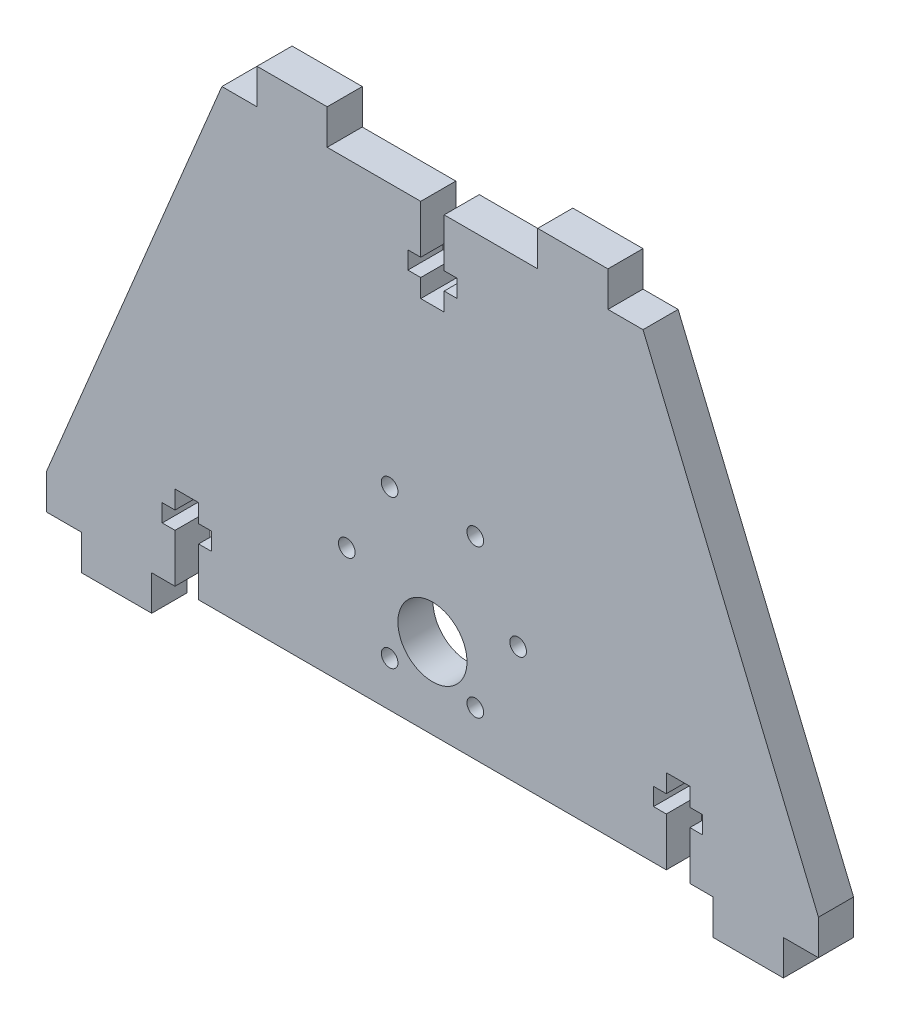
SolidWorks part; units mm, degrees
ref_plane "Front Plane" through (0, 0, 0) normal (0, 0, 1) x (1, 0, 0)
ref_plane "Top Plane" through (0, 0, 0) normal (0, 1, 0) x (1, 0, 0)
ref_plane "Right Plane" through (0, 0, 0) normal (1, 0, 0) x (0, 0, -1)
sketch "Sketch1" plane through (0, 0, 0) normal (0, 0, 1) x (1, 0, 0)
  line L1 (-69.85, 41.275) -> (69.85, 41.275)
  line L2 (-69.85, 41.275) -> (-69.85, -41.275)
  line L3 (-69.85, -41.275) -> (69.85, -41.275)
  line L4 (69.85, 41.275) -> (69.85, -41.275)
  line L5 (-69.85, 41.275) -> (69.85, -41.275) construction
  line L6 (-69.85, -41.275) -> (69.85, 41.275) construction
  point P0 (0, 0)
  dimension "D1" = 82.55
  dimension "D2" = 139.7
extrude "Boss-Extrude1" add sketch "Sketch1" along normal blind 6.35
sketch "Sketch2" plane through (0, 0, 0) normal (0, 0, -1) x (-1, 0, 0)
  line L0 (69.85, -41.275) -> (-69.85, -41.275) construction
  line L1 (-63.5, -41.275) -> (-50.8, -41.275)
  line L2 (-63.5, -41.275) -> (-63.5, -47.625)
  line L3 (-63.5, -47.625) -> (-50.8, -47.625)
  line L4 (-50.8, -41.275) -> (-50.8, -47.625)
  line L5 (-69.85, -41.275) -> (-69.85, 41.275) construction
  line L6 (-69.85, 41.275) -> (69.85, 41.275) construction
  line L7 (-31.75, 41.275) -> (-19.05, 41.275)
  line L8 (-31.75, 41.275) -> (-31.75, 47.625)
  line L9 (-31.75, 47.625) -> (-19.05, 47.625)
  line L10 (-19.05, 41.275) -> (-19.05, 47.625)
  dimension "D1" = 6.35
  dimension "D2" = 12.7
  dimension "D3" = 6.35
  dimension "D4" = 6.35
  dimension "D5" = 12.7
  dimension "D6" = 38.1
extrude "Boss-Extrude2" add sketch "Sketch2" against normal blind 6.35
sketch "Sketch3" plane through (0, 0, 0) normal (0, 0, -1) x (-1, 0, 0)
  line L1 (-46.5836, -41.275) -> (-46.5836, -32.512)
  line L2 (69.85, -41.275) -> (-50.8, -41.275) construction
  line L3 (-46.5836, -32.512) -> (-48.895, -32.512)
  line L4 (-48.895, -32.512) -> (-48.895, -29.337)
  line L5 (-48.895, -29.337) -> (-46.5836, -29.337)
  line L6 (-46.5836, -29.337) -> (-46.5836, -26.035)
  line L7 (-46.5836, -26.035) -> (-42.3164, -26.035)
  line L8 (-44.45, -26.035) -> (-44.45, -41.275) construction
  line L9 (-42.3164, -41.275) -> (-46.5836, -41.275)
  line L10 (-63.5, -47.625) -> (-50.8, -47.625) construction
  line L11 (-42.3164, -29.337) -> (-42.3164, -26.035)
  line L12 (-40.005, -29.337) -> (-42.3164, -29.337)
  line L13 (-40.005, -32.512) -> (-40.005, -29.337)
  line L14 (-42.3164, -32.512) -> (-40.005, -32.512)
  line L15 (-42.3164, -41.275) -> (-42.3164, -32.512)
  line L16 (-50.8, -47.625) -> (-50.8, -41.275) construction
  dimension "D1" = 21.59
  dimension "D2" = 3.302
  dimension "D3" = 3.175
  dimension "D4" = 4.2672
  dimension "D5" = 4.445
  dimension "D6" = 6.35
extrude "Cut-Extrude1" cut sketch "Sketch3" against normal blind 6.35
sketch "Sketch7" plane through (0, 0, 0) normal (0, 0, -1) x (-1, 0, 0)
  line L0 (-38.1, 41.275) -> (-69.85, -34.925)
  line L1 (-69.85, 41.275) -> (-31.75, 41.275) construction
  line L2 (-69.85, -41.275) -> (-69.85, 41.275) construction
  line L3 (-69.85, -34.925) -> (-69.85, 41.275)
  line L4 (-69.85, 41.275) -> (-38.1, 41.275)
  line L5 (-31.75, 47.625) -> (-31.75, 41.275) construction
  dimension "D1" = 6.35
  dimension "D2" = 6.35
extrude "Cut-Extrude8" cut sketch "Sketch7" against normal blind 6.35
mirror "Mirror2" about plane through (0, 0, 0) normal (1, 0, 0) of "Cut-Extrude8", "Boss-Extrude2"
mirror "Mirror4" about plane through (0, 0, 0) normal (1, 0, 0) of "Cut-Extrude1"
sketch "Sketch4" plane through (0, 0, 0) normal (0, 0, -1) x (-1, 0, 0)
  line L0 (0, 41.275) -> (0, 0) construction
  line L2 (2.1209, 41.275) -> (-2.1209, 41.275)
  line L3 (-2.1209, 41.275) -> (-2.1209, 32.512)
  line L4 (-2.1209, 32.512) -> (-4.445, 32.512)
  line L5 (-4.445, 32.512) -> (-4.445, 29.337)
  line L6 (-4.445, 29.337) -> (-2.1209, 29.337)
  line L7 (-2.1209, 29.337) -> (-2.1209, 26.035)
  line L8 (-2.1209, 26.035) -> (2.1209, 26.035)
  line L10 (2.1209, 29.337) -> (2.1209, 26.035)
  line L11 (4.445, 29.337) -> (2.1209, 29.337)
  line L12 (4.445, 32.512) -> (4.445, 29.337)
  line L13 (2.1209, 32.512) -> (4.445, 32.512)
  line L14 (2.1209, 41.275) -> (2.1209, 32.512)
  line L15 (-19.05, 47.625) -> (-31.75, 47.625) construction
  line L16 (-19.05, 41.275) -> (19.05, 41.275) construction
  point P15 (0, 26.035)
  dimension "D1" = 2.1209
  dimension "D2" = 4.445
  dimension "D3" = 21.59
  dimension "D4" = 3.302
  dimension "D5" = 3.175
extrude "Cut-Extrude2" cut sketch "Sketch4" against normal blind 6.35
sketch "Sketch5" plane through (0, 0, 0) normal (0, 0, -1) x (-1, 0, 0)
  circle A0 centre (-15.5, -7) radius 1.25 construction
  circle A1 centre (0, -14) radius 6 construction
  circle A2 centre (-7.75, -20.4234) radius 1.25 construction
  circle A3 centre (-7.75, 6.4234) radius 1.25 construction
  circle A4 centre (7.75, 6.4234) radius 1.25 construction
  circle A5 centre (15.5, -7) radius 1.25 construction
  circle A6 centre (7.75, -20.4234) radius 1.25 construction
  circle A7 centre (-15.5, -7) radius 1.25 construction
  circle A8 centre (0, -14) radius 6 construction
  circle A9 centre (-7.75, -20.4234) radius 1.25 construction
  circle A10 centre (-7.75, 6.4234) radius 1.25 construction
  circle A11 centre (7.75, 6.4234) radius 1.25 construction
  circle A12 centre (15.5, -7) radius 1.25 construction
  circle A13 centre (7.75, -20.4234) radius 1.25 construction
  circle A14 centre (-15.5, -7) radius 1.504
  circle A15 centre (0, -14) radius 6.254
  circle A16 centre (-7.75, -20.4234) radius 1.504
  circle A17 centre (-7.75, 6.4234) radius 1.504
  circle A18 centre (7.75, 6.4234) radius 1.504
  circle A19 centre (15.5, -7) radius 1.504
  circle A20 centre (7.75, -20.4234) radius 1.504
  circle A21 centre (-15.5, -19.7) radius 1.504
  circle A22 centre (0, -26.7) radius 6.254
  circle A23 centre (-7.75, -33.1234) radius 1.504
  circle A24 centre (-7.75, -6.2766) radius 1.504
  circle A25 centre (7.75, -6.2766) radius 1.504
  circle A26 centre (15.5, -19.7) radius 1.504
  circle A27 centre (7.75, -33.1234) radius 1.504
  circle A28 centre (-15.5, -19.7) radius 1.25 construction
  circle A29 centre (0, -26.7) radius 6 construction
  circle A30 centre (-7.75, -33.1234) radius 1.25 construction
  circle A31 centre (-7.75, -6.2766) radius 1.25 construction
  circle A32 centre (7.75, -6.2766) radius 1.25 construction
  circle A33 centre (15.5, -19.7) radius 1.25 construction
  circle A34 centre (7.75, -33.1234) radius 1.25 construction
  dimension "D2" = 2
  dimension "D1" = 0.254
extrude "Cut-Extrude9" cut sketch "Sketch5" against normal blind 6.35 contours A22 | A21 | A24 | A25 | A26 | A27 | A23
